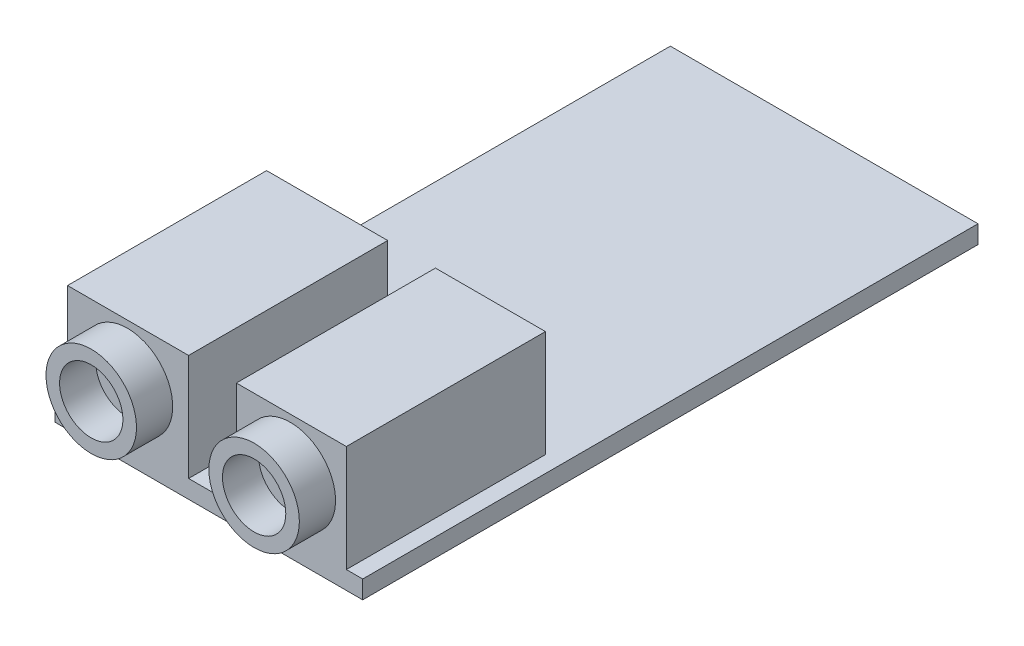
SolidWorks part; units mm, degrees
ref_plane "Ön Düzlem" through (0, 0, 0) normal (0, 0, 1) x (1, 0, 0)
ref_plane "Üst Düzlem" through (0, 0, 0) normal (0, 1, 0) x (1, 0, 0)
ref_plane "Sağ Düzlem" through (0, 0, 0) normal (1, 0, 0) x (0, 0, -1)
sketch "Çizim1" plane through (0, 0, 0) normal (0, 1, 0) x (1, 0, 0)
  line L0 (-8.5, 17) -> (8.5, -17) construction
  line L1 (-8.5, -17) -> (8.5, -17)
  line L2 (-8.5, -17) -> (-8.5, 17)
  line L3 (-8.5, 17) -> (8.5, 17)
  line L4 (8.5, -17) -> (8.5, 17)
  dimension "D1" = 34
  dimension "D2" = 17
extrude "Yükseklik-Ekstrüzyon1" add sketch "Çizim1" along normal blind 1
sketch "Çizim2" plane through (0, 0, 17) normal (0, 0, 1) x (1, 0, 0)
  line L0 (-8.5, 1) -> (8.5, 1) construction
  line L2 (0, 0) -> (0, 8.0266) construction
  line L3 (-8.5, 0) -> (8.5, 0) construction
  circle A0 centre (-4.5, 4) radius 2.5
  circle A1 centre (4.5, 4) radius 2.5
  circle A2 centre (-4.5, 4) radius 1.75
  circle A3 centre (4.5, 4) radius 1.75
  dimension "D1" = 3
  dimension "D2" = 9
extrude "Yükseklik-Ekstrüzyon2" add sketch "Çizim2" along normal blind 2 separate body
sketch "Çizim3" plane through (0, 0, 17) normal (0, 0, 1) x (1, 0, 0)
  line L0 (-8.5, 1) -> (8.5, 1) construction
  line L1 (-7.8102, 1) -> (-1.1196, 1)
  line L2 (-7.8102, 1) -> (-7.8102, 6.8886)
  line L3 (-7.8102, 6.8886) -> (-1.1196, 6.8886)
  line L4 (-1.1196, 1) -> (-1.1196, 6.8886)
  line L6 (1.5194, 1) -> (7.597, 1)
  line L7 (1.5194, 1) -> (1.5194, 6.8886)
  line L8 (1.5194, 6.8886) -> (7.597, 6.8886)
  line L9 (7.597, 1) -> (7.597, 6.8886)
extrude "Yükseklik-Ekstrüzyon3" add sketch "Çizim3" against normal blind 11
